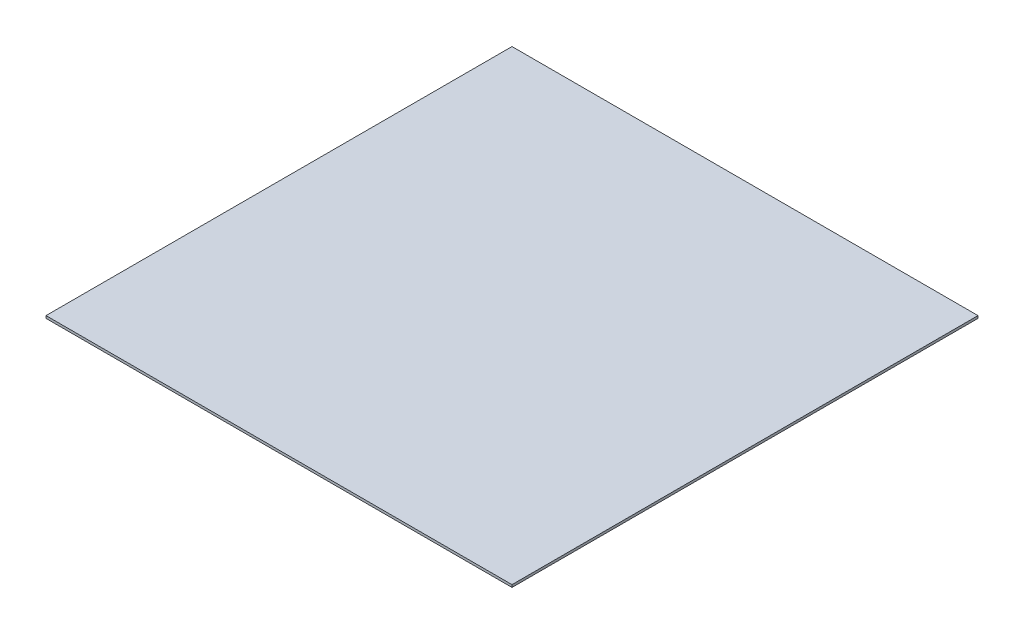
SolidWorks part; units mm, degrees
ref_plane "Front Plane" through (0, 0, 0) normal (0, 0, 1) x (1, 0, 0)
ref_plane "Top Plane" through (0, 0, 0) normal (0, 1, 0) x (1, 0, 0)
ref_plane "Right Plane" through (0, 0, 0) normal (1, 0, 0) x (0, 0, -1)
sketch "Sketch1" plane through (0, 0, 0) normal (0, 1, 0) x (1, 0, 0)
  line L1 (0, 0) -> (19000, 0)
  line L2 (0, 0) -> (0, -19000)
  line L3 (0, -19000) -> (19000, -19000)
  line L4 (19000, 0) -> (19000, -19000)
  dimension "D1" = 19000
  dimension "D2" = 19000
extrude "Boss-Extrude1" add sketch "Sketch1" along normal blind 100
